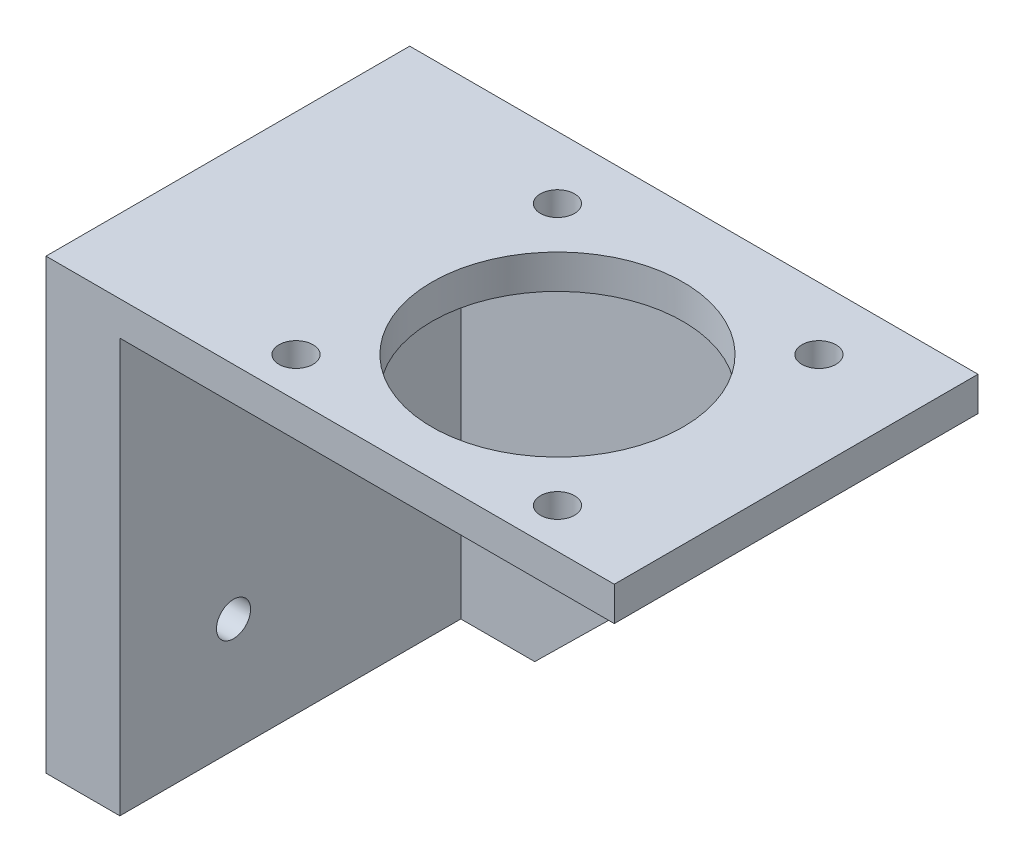
SolidWorks part; units mm, degrees
ref_plane "Front Plane" through (0, 0, 0) normal (0, 0, 1) x (1, 0, 0)
ref_plane "Top Plane" through (0, 0, 0) normal (0, 1, 0) x (1, 0, 0)
ref_plane "Right Plane" through (0, 0, 0) normal (1, 0, 0) x (0, 0, -1)
sketch "Croquis1" plane through (0, 0, 0) normal (0, 0, 1) x (1, 0, 0)
  line L1 (-1.5, 19.7) -> (1.5, 19.7)
  line L2 (-1.5, 19.7) -> (-1.5, -19.7)
  line L3 (-1.5, -19.7) -> (1.5, -19.7)
  line L4 (1.5, 19.7) -> (1.5, -19.7)
  line L5 (-1.5, 19.7) -> (1.5, -19.7) construction
  line L6 (-1.5, -19.7) -> (1.5, 19.7) construction
  line L7 (-1.5, 19.7) -> (38.5, 19.7)
  line L8 (-1.5, 19.7) -> (-1.5, 16.7)
  line L9 (-1.5, 16.7) -> (38.5, 16.7)
  line L10 (38.5, 19.7) -> (38.5, 16.7)
  line L11 (-1.5, 19.7) -> (38.5, 16.7) construction
  line L12 (-1.5, 16.7) -> (38.5, 19.7) construction
  point P0 (0, 0)
  point P5 (18.5, 18.2)
  dimension "D1" = 3
  dimension "D2" = 39.4
  dimension "D3" = 3
  dimension "D4" = 40
extrude "Saliente-Extruir1" add sketch "Croquis1" along normal blind 30 contours L9 L2 L3 L4 | L2 L9 L4 L1 | L10 L7 L4 L9
sketch "Croquis3" plane through (0, 19.7, 0) normal (0, 1, 0) x (1, 0, 0)
  line L0 (-1.5, 0) -> (38.5, 0) construction
  line L1 (38.5, -30) -> (38.5, 0) construction
  line L2 (18.5, -15) -> (0, -15) construction
  line L3 (-1.5, -30) -> (38.5, -30) construction
  circle A0 centre (18.5, -15) radius 11.05
  circle A1 centre (18.5, -15) radius 16.265 construction
  circle A2 centre (6.9978, -26.5) radius 1.5
  circle A3 centre (30.0022, -26.5) radius 1.5
  circle A4 centre (30.0022, -3.5) radius 1.5
  circle A5 centre (6.9978, -3.5) radius 1.5
  dimension "D1" = 22.1
  dimension "D4" = 32.53
  dimension "D5" = 3
  dimension "D6" = 3
  dimension "D2" = 15
  dimension "D3" = 20
  dimension "D7" = 3.5
  dimension "D8" = 11.5
extrude "Cortar-Extruir2" cut sketch "Croquis3" against normal blind 30
ref_plane "Plano1" through (1.5, 16.7, 30) normal (0, 0, -1) x (-1, 0, 0)
sketch "Croquis6" plane through (0, 0, 0) normal (0, 0, 1) x (1, 0, 0)
  line L0 (-1.5, 19.7) -> (38.5, 19.7)
  line L2 (-1.5, -19.7) -> (-1.5, 19.7)
  line L3 (38.5, 19.7) -> (38.5, 16.7)
  line L4 (38.5, 16.7) -> (1.5, -19.7)
  line L5 (1.5, -19.7) -> (-1.5, -19.7)
extrude "Saliente-Extruir3" add sketch "Croquis6" against normal blind 2
sketch "Croquis8" plane through (-1.5, 0, 0) normal (-1, 0, 0) x (0, 0, 1)
  line L0 (-2, 19.7) -> (30, 19.7)
  line L1 (30, 19.7) -> (30, -19.7)
  line L2 (30, -19.7) -> (-2, -19.7)
  line L3 (-2, -19.7) -> (-2, 19.7)
extrude "Saliente-Extruir4" add sketch "Croquis8" along normal blind 10
sketch "Croquis9" plane through (0, 0, 30) normal (0, 0, 1) x (1, 0, 0)
  line L0 (1.5, -19.7) -> (-5, -19.7)
  line L1 (-11.5, -19.7) -> (1.5, -19.7) construction
  line L2 (-5, -19.7) -> (-5, 16.7)
  line L3 (-5, 16.7) -> (1.5, 16.7)
  line L4 (1.5, 16.7) -> (1.5, -19.7)
extrude "Cortar-Extruir4" cut sketch "Croquis9" against normal blind 30
sketch "Croquis10" plane through (-11.5, 0, 0) normal (-1, 0, 0) x (0, 0, 1)
  line L0 (30, -19.7) -> (30, 19.7) construction
  line L1 (-2, -19.7) -> (30, -19.7) construction
  line L2 (-2, 19.7) -> (-2, -19.7) construction
  line L3 (30, 19.7) -> (-2, 19.7) construction
  circle A1 centre (5, 14.7) radius 1.5
  circle A4 centre (20, 14.7) radius 1.5
  circle A5 centre (20, -9.7) radius 1.5
  dimension "D2" = 3
  dimension "D6" = 5
  dimension "D7" = 3
  dimension "D8" = 5
  dimension "D9" = 10
  dimension "D10" = 10
  dimension "D11" = 3
  dimension "D5" = 7
  dimension "D13" = 10
extrude "Cortar-Extruir5" cut sketch "Croquis10" against normal blind 10
